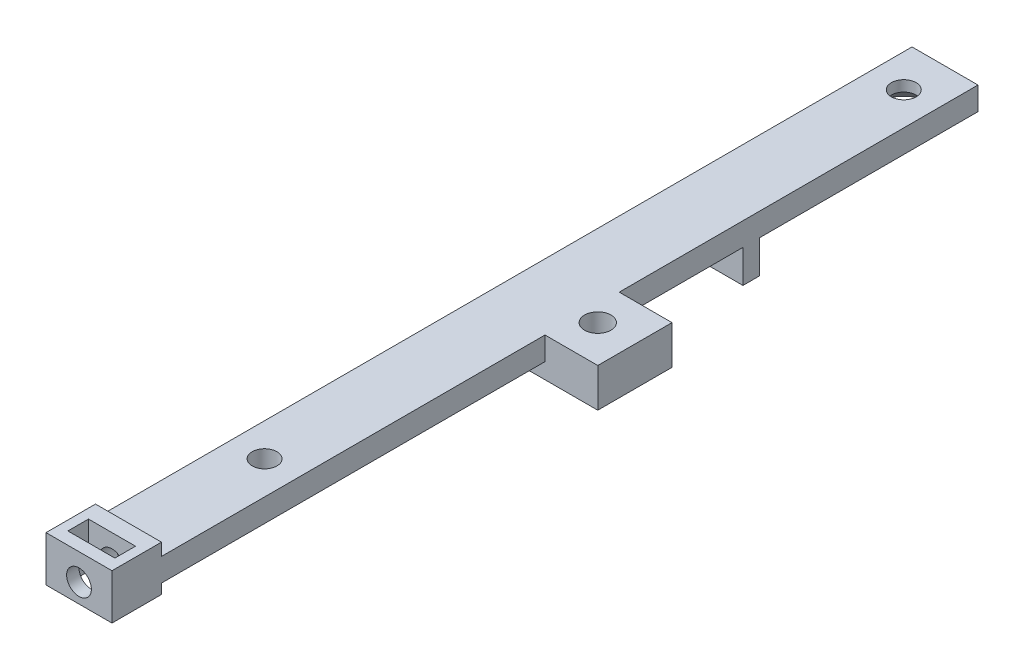
SolidWorks part; units mm, degrees
ref_plane "Front Plane" through (0, 0, 0) normal (0, 0, 1) x (1, 0, 0)
ref_plane "Top Plane" through (0, 0, 0) normal (0, 1, 0) x (1, 0, 0)
ref_plane "Right Plane" through (0, 0, 0) normal (1, 0, 0) x (0, 0, -1)
sketch "Sketch2" plane through (0, 0, 0) normal (0, 1, 0) x (1, 0, 0)
  line L0 (0, 0) -> (0, 37.5227)
  line L1 (0, 37.5227) -> (0, 55)
  line L2 (0, 55) -> (0, 105)
  line L3 (0, 105) -> (4, 105)
  line L6 (8, 0) -> (8, 37.5227)
  line L9 (8, 105) -> (4, 105)
  line L10 (8, 55) -> (8, 105)
  line L11 (8, 37.5227) -> (8, 55)
  line L12 (8, 0) -> (0, 0)
  line L14 (4, 105) -> (4, 0) construction
  dimension "D1" = 105
  dimension "D3" = 4
  dimension "D5" = 4
  dimension "D6" = 50
extrude "Boss-Extrude1" add sketch "Sketch2" along normal blind 2.8
sketch "Sketch3" plane through (0, 2.8, 0) normal (0, 1, 0) x (1, 0, 0)
  line L1 (4, 105) -> (4, 100) construction
  line L2 (8, 105) -> (0, 105) construction
  line L3 (4, 105) -> (4, 100) construction
  line L4 (8, 105) -> (0, 105) construction
  circle A0 centre (4, 100) radius 1.5
  dimension "D2" = 3
  dimension "D1" = 5
extrude "Cut-Extrude1" cut sketch "Sketch3" against normal up to next
chamfer "Chamfer1" distance 1.5 angle 45 1 edges at (4, 0, -101.5)
sketch "Sketch6" plane through (0, 0, 0) normal (0, -1, 0) x (-1, 0, 0)
  line L0 (-8, 0) -> (-8, 105) construction
  line L1 (0, 0) -> (-8, 0)
  line L2 (0, 0) -> (0, 6)
  line L3 (0, 6) -> (-8, 6)
  line L4 (-8, 0) -> (-8, 6)
  dimension "D1" = 6
extrude "Boss-Extrude3" add sketch "Sketch6" against normal blind 4.3 and the other way blind 1.2
sketch "Sketch7" plane through (0, 0, 0) normal (0, 0, 1) x (1, 0, 0)
  line L0 (4, 1.1) -> (4, -1.2) construction
  line L2 (8, -1.2) -> (0, -1.2) construction
  circle A0 centre (4, 1.1) radius 1.5
  dimension "D1" = 3
  dimension "D2" = 2.3
extrude "Cut-Extrude3" cut sketch "Sketch7" against normal up to surface (6 mm away) up to face at (4, -0.6, -6)
sketch "Sketch8" plane through (0, 4.3, 0) normal (0, 1, 0) x (1, 0, 0)
  line L0 (4, 1.5) -> (4, 0) construction
  line L1 (8, 0) -> (0, 0) construction
  line L2 (1.15, 4) -> (6.85, 4)
  line L3 (1.15, 4) -> (1.15, 1.5)
  line L4 (1.15, 1.5) -> (6.85, 1.5)
  line L5 (6.85, 4) -> (6.85, 1.5)
  dimension "D1" = 1.5
  dimension "D2" = 2.5
  dimension "D3" = 5.7
extrude "Cut-Extrude4" cut sketch "Sketch8" against normal blind 7
sketch "Sketch9" plane through (0, 2.8, 0) normal (0, 1, 0) x (1, 0, 0)
  line L1 (14.4, 61.5) -> (0, 61.5)
  line L2 (14.4, 61.5) -> (14.4, 52.5)
  line L3 (14.4, 52.5) -> (0, 52.5)
  line L4 (0, 61.5) -> (0, 52.5)
  line L6 (8, 105) -> (0, 105) construction
  line L7 (8, 6) -> (8, 105) construction
  line L8 (0, 105) -> (0, 6) construction
  dimension "D1" = 6.4
  dimension "D2" = 9
  dimension "D3" = 43.5
extrude "Boss-Extrude4" add sketch "Sketch9" against normal blind 4.7
sketch "Sketch10" plane through (0, -1.9, 0) normal (0, -1, 0) x (1, 0, 0)
  line L0 (9.9, -57) -> (0, -57) construction
  line L1 (0, -61.5) -> (0, -52.5) construction
  line L2 (14.4, -52.5) -> (14.4, -61.5) construction
  line L3 (4, -52.5) -> (4, -22.5) construction
  line L4 (8, -52.5) -> (0, -52.5) construction
  circle A0 centre (9.9, -57) radius 1.6
  circle A1 centre (4, -22.5) radius 1.5
  dimension "D1" = 3.2
  dimension "D2" = 4.5
  dimension "D4" = 3
  dimension "D3" = 30
extrude "Cut-Extrude5" cut sketch "Sketch10" against normal up to next
sketch "Sketch11" plane through (0, 0, 0) normal (0, -1, 0) x (1, 0, 0)
  line L0 (8, -61.5) -> (8, -105) construction
  line L1 (8, -78.5) -> (0, -78.5)
  line L2 (8, -78.5) -> (8, -76.5)
  line L3 (8, -76.5) -> (0, -76.5)
  line L4 (0, -78.5) -> (0, -76.5)
  line L5 (0, -105) -> (0, -61.5) construction
  line L6 (0, -61.5) -> (8, -61.5) construction
  dimension "D1" = 15
  dimension "D2" = 2
extrude "Boss-Extrude5" add sketch "Sketch11" along normal blind 4
